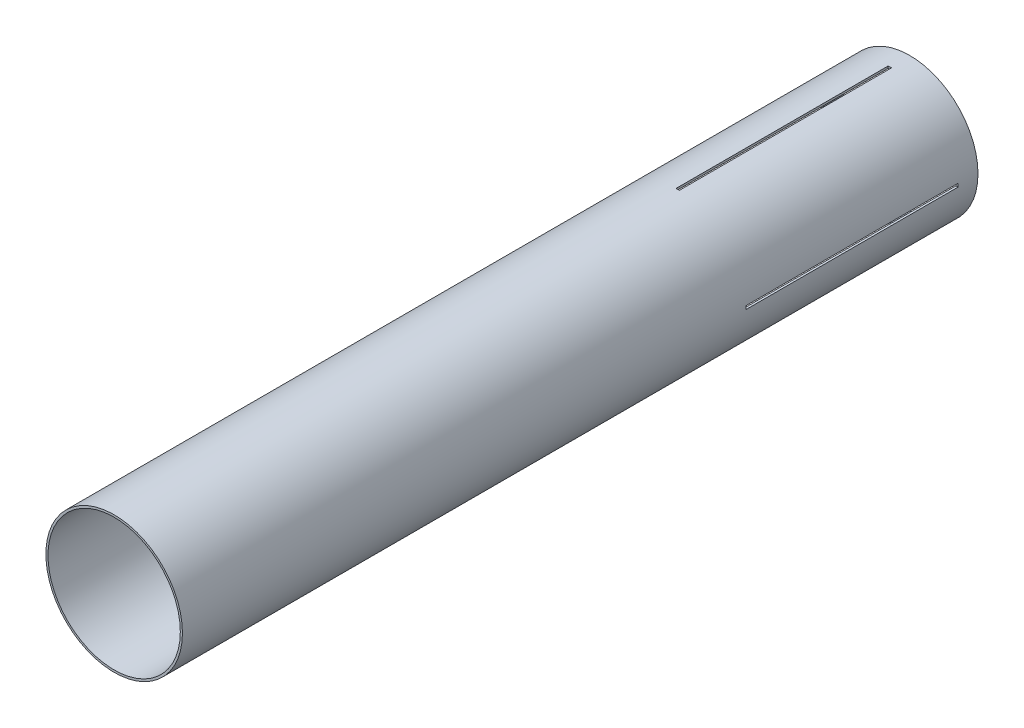
SolidWorks part; units mm, degrees
ref_plane "Front Plane" through (0, 0, 0) normal (0, 0, 1) x (1, 0, 0)
ref_plane "Top Plane" through (0, 0, 0) normal (0, 1, 0) x (1, 0, 0)
ref_plane "Right Plane" through (0, 0, 0) normal (1, 0, 0) x (0, 0, -1)
sketch "Sketch1" plane through (0, 0, 0) normal (0, 0, 1) x (1, 0, 0)
  circle A0 centre (0, 0) radius 65.405
  circle A1 centre (0, 0) radius 63.373
  dimension "D1" = 126.746
  dimension "D2" = 130.81
extrude "Boss-Extrude1" add sketch "Sketch1" along normal mid plane 762
sketch "Sketch3" plane through (0, 0, 0) normal (0, 1, 0) x (1, 0, 0)
  line L0 (65.405, 381) -> (-65.405, 381) construction
  line L1 (1.5875, 158.75) -> (-1.5875, 158.75)
  line L2 (1.5875, 158.75) -> (1.5875, 361.95)
  line L3 (1.5875, 361.95) -> (-1.5875, 361.95)
  line L4 (-1.5875, 158.75) -> (-1.5875, 361.95)
  line L5 (1.5875, 158.75) -> (-1.5875, 361.95) construction
  line L6 (1.5875, 361.95) -> (-1.5875, 158.75) construction
  line L7 (65.405, 381) -> (-65.405, 381) construction
  point P0 (0, 260.35)
  dimension "D2" = 203.2
  dimension "D3" = 19.05
extrude "Cut-Extrude1" cut sketch "Sketch3" along normal through all
pattern_circular "CirPattern1" count 4 over 360 about axis through (0, 0, 0) along (0, 0, 1) of "Cut-Extrude1"
equation "\"AIRFRAME_OD\"= 5.15in"
equation "\"AIRFRAME_ID\"= 4.99in"
equation "\"FLAT_T\"= 0.125in"
equation "\"NOSE_EXP_L\"= 27in"
equation "\"NOSE_SHOULDER_L\"= 5in"
equation "\"MAIN_L\"= 30in"
equation "\"RECO_COUP_L\"= 10in"
equation "\"RECO_SWITCH_L\"= 2in"
equation "\"DROGUE_L\"= 20in"
equation "\"ATS_FORE_COUP_L\"= 5.5in"
equation "\"ATS_AFT_COUP_L\"= 4.5in"
equation "\"LOWER_L\"= 30in"
equation "\"FIN_N\"= 4"
equation "\"CR_AFT_X\"= 0.5in"
equation "\"CR_FORE_X\"= 9.25in"
equation "\"D1@Sketch1\"=\"AIRFRAME_ID\""
equation "\"D2@Sketch1\"=\"AIRFRAME_OD\""
equation "\"D1@Boss-Extrude1\"=\"LOWER_L\""
equation "\"FIN_ROOT\"= 8in"
equation "\"FIN_X\"= 0.75in"
equation "\"MOTOR_OD\"= 3.091in"
equation "\"MOTOR_ID\"= 3.00in"
equation "\"D1@Sketch3\"=\"FLAT_T\""
equation "\"D2@Sketch3\"=\"FIN_ROOT\""
equation "\"D3@Sketch3\"=\"FIN_X\""
equation "\"D1@CirPattern1\"=\"FIN_N\""
equation "\"COUPLER_OD\"= 4.998in"
equation "\"COUPLER_ID\"= 4.85in"
equation "\"RECO_ROD_X\"= 3.5in"
equation "\"ATS_ROD_X\"= 3.75in"
equation "\"MOTOR_L\"= 14in"
equation "\"MOTOR_LOWER_X\"= 2in"
